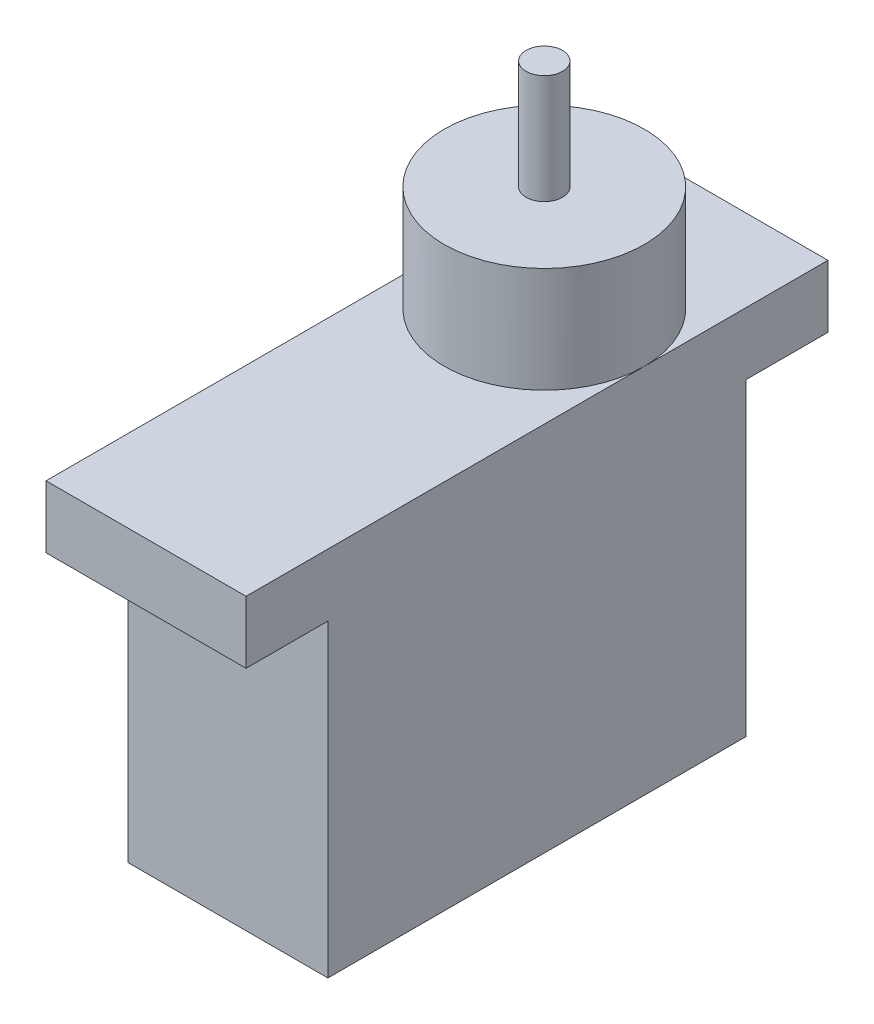
SolidWorks part; units mm, degrees
ref_plane "Plan de face" through (0, 0, 0) normal (0, 0, 1) x (1, 0, 0)
ref_plane "Plan de dessus" through (0, 0, 0) normal (0, 1, 0) x (1, 0, 0)
ref_plane "Plan de droite" through (0, 0, 0) normal (1, 0, 0) x (0, 0, -1)
sketch "Esquisse1" plane through (0, 0, 0) normal (1, 0, 0) x (0, 0, -1)
  line L0 (0, 17) -> (4.5, 17)
  line L1 (0, 0) -> (-23, 0)
  line L2 (0, 0) -> (0, 17)
  line L4 (-23, 0) -> (-23, 17)
  line L5 (-27.5, 20.43) -> (4.5, 20.43)
  line L6 (-27.5, 20.43) -> (-27.5, 17)
  line L7 (-27.5, 17) -> (-23, 17)
  line L8 (4.5, 20.43) -> (4.5, 17)
  dimension "D1" = 23
  dimension "D2" = 17
  dimension "D3" = 32
  dimension "D4" = 3.43
extrude "Boss.-Extru.1" add sketch "Esquisse1" along normal blind 11
sketch "Esquisse2" plane through (0, 20.43, 0) normal (0, 1, 0) x (1, 0, 0)
  line L0 (11, -27.5) -> (0, -27.5) construction
  circle A0 centre (5.5, -5.6) radius 5.5
  point P0 (5.5, -27.5)
  dimension "D1" = 21.9
extrude "Boss.-Extru.2" add sketch "Esquisse2" along normal blind 5.8
sketch "Esquisse7" plane through (0, 26.23, 0) normal (0, 1, 0) x (1, 0, 0)
  circle A0 centre (5.5, -5.6) radius 1
  arc A1 (11, -5.6) -> (0, -5.6) centre (5.5, -5.6) ccw construction
  dimension "D1" = 2
extrude "Boss.-Extru.3" add sketch "Esquisse7" along normal blind 6
